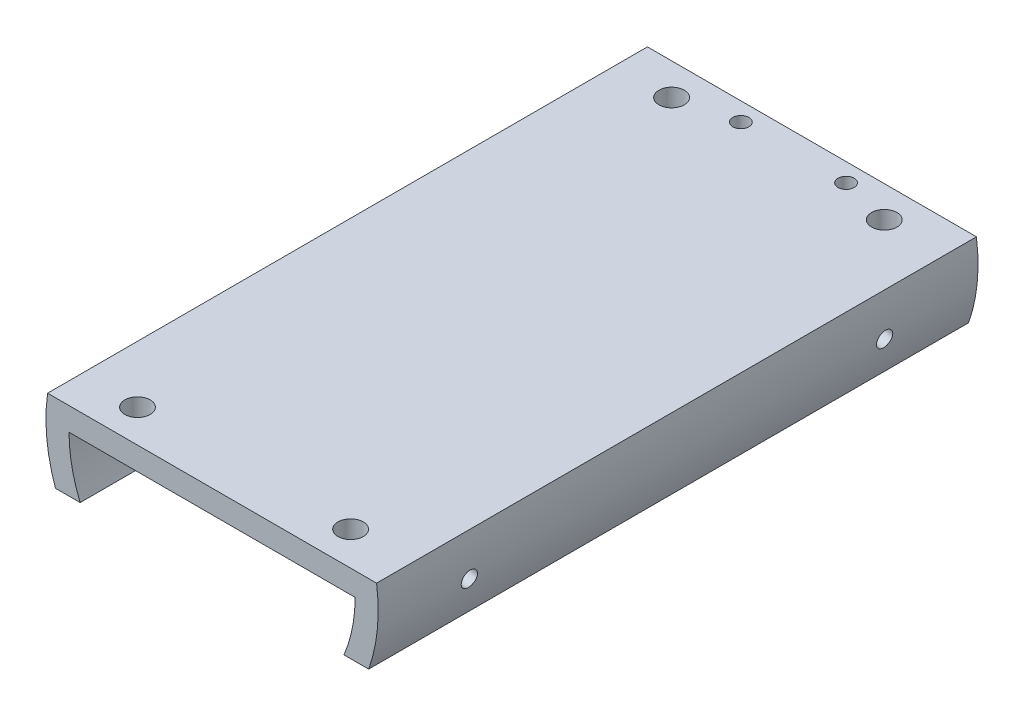
SolidWorks part; units mm, degrees
material "PET"
ref_plane "Front Plane" through (0, 0, 0) normal (0, 0, 1) x (1, 0, 0)
ref_plane "Top Plane" through (0, 0, 0) normal (0, 1, 0) x (1, 0, 0)
ref_plane "Right Plane" through (0, 0, 0) normal (1, 0, 0) x (0, 0, -1)
sketch "Sketch1" plane through (0, 0, 0) normal (0, 0, 1) x (1, 0, 0)
  line L0 (18, 0) -> (-18, 0)
  line L1 (18, 2.5) -> (-18, 2.5)
  line L2 (0, 0) -> (16.3135, -7.6071)
  line L3 (0, 0) -> (-16.3135, -7.6071)
  circle A0 centre (0, 0) radius 18
  circle A1 centre (0, 0) radius 15.5
  dimension "D1" = 36
  dimension "D4" = 25
  dimension "D5" = 25
  dimension "D2" = 2.5
  dimension "D3" = 2.5
extrude "Boss-Extrude1" add sketch "Sketch1" along normal blind 65 contours A1 L2 A0 L0 | A1 L0 A0 L1 | L0 A1 L1 | A1 L0 A0 L3 | A1 L1 A0 L0
sketch "Sketch2" plane through (0, 2.5, 0) normal (0, 1, 0) x (1, 0, 0)
  circle A0 centre (11.2395, -3.3946) radius 1.375
  circle A1 centre (-11.7605, -3.4431) radius 1.375
  circle A2 centre (11.3618, -61.3474) radius 1.375
  circle A3 centre (-11.638, -61.443) radius 1.375
  dimension "D1" = 2.75
  dimension "D2" = 2.75
  dimension "D3" = 2.75
  dimension "D4" = 2.75
extrude "Cut-Extrude1" cut sketch "Sketch2" against normal up to next
sketch "Sketch3" plane through (0, 0, 65) normal (0, 0, 1) x (1, 0, 0)
  line L0 (15.5, 0) -> (-15.5, 0) construction
  line L1 (-9, -6) -> (9, -6)
  line L2 (-9, -9) -> (9, -9)
  line L3 (-9, -9) -> (-9, 0)
  line L4 (-9, 0) -> (9, 0)
  line L5 (9, -9) -> (9, 0)
  circle A0 centre (0, -9) radius 9
  line M14 (-15.5, 0) -> (15.5, 0)
  dimension "D1" = 18
  dimension "D2" = 6
extrude "Boss-Extrude2" add sketch "Sketch3" against normal blind 65 contours A0 L3 L1 M14 | A0 L1 L5 L4
ref_plane "Plane1" through (-17.7265, -3.1257, 0) normal (-0.9848, -0.1736, 0) x (0, 0, -1)
sketch "Sketch4" [suppressed] plane through (-17.7265, -3.1257, 0) normal (-0.9848, -0.1736, 0) x (0, 0, -1)
  line L0 (-65, -5.5574) -> (0, -5.5574) construction
  line L1 (-65, 4.6587) -> (-65, -5.5574) construction
  circle A0 centre (-60, -1.5574) radius 0.875
  circle A1 centre (-5, -1.5574) radius 0.875
  dimension "D1" = 1.75
  dimension "D3" = 5
  dimension "D2" = 4
  dimension "D4" = 2
sketch "Sketch5" plane through (0, 2.5, 0) normal (0, 1, 0) x (1, 0, 0)
  circle A0 centre (-5.7, -2) radius 0.875
  circle A1 centre (5.7, -2) radius 0.875
  dimension "D1" = 1.75
  dimension "D2" = 1.75
extrude "Cut-Extrude3" cut sketch "Sketch5" against normal up to next
sketch "Sketch6" plane through (-17.7265, -3.1257, 0) normal (-0.9848, -0.1736, 0) x (0, 0, -1)
  line L0 (-65, -5.5574) -> (0, -5.5574) construction
  line L1 (-65, 4.6587) -> (-65, -5.5574) construction
  line L2 (0, -5.5574) -> (0, 4.6587) construction
  circle A0 centre (-55, -1.0574) radius 0.875
  circle A1 centre (-10, -1.0574) radius 0.875
  dimension "D1" = 1.75
  dimension "D3" = 10
  dimension "D4" = 1.75
  dimension "D2" = 4.5
  dimension "D5" = 10
  dimension "D6" = 4.5
extrude "Cut-Extrude4" cut sketch "Sketch6" against normal up to next
mirror "Mirror1" about plane through (0, 0, 0) normal (1, 0, 0) of "Cut-Extrude4"
ref_plane "Plane2" through (0, 0, 32.5) normal (0, 0, 1) x (1, 0, 0)
sketch "Sketch8" plane through (0, 0, 32.5) normal (0, 0, 1) x (1, 0, 0)
  line L0 (-16.9706, -6) -> (16.9706, -6)
  line L9 (14.0478, -6.5506) -> (16.3135, -7.6071)
  line L10 (17.8255, 2.5) -> (-17.8255, 2.5)
  line L11 (-16.3135, -7.6071) -> (-14.0478, -6.5506)
  line L12 (-15.5, 0) -> (-9, 0)
  line L13 (-9, 0) -> (-9, -6)
  line L14 (-9, -6) -> (-8.4853, -6)
  line L15 (8.4853, -6) -> (9, -6)
  line L16 (9, -6) -> (9, 0)
  line L17 (9, 0) -> (15.5, 0)
  line L18 (14.0478, -6.5506) -> (16.3135, -7.6071)
  line L19 (17.8255, 2.5) -> (-17.8255, 2.5)
  line L20 (-16.3135, -7.6071) -> (-14.0478, -6.5506)
  line L21 (-15.5, 0) -> (-9, 0)
  line L22 (-9, 0) -> (-9, -6)
  line L23 (-9, -6) -> (-8.4853, -6)
  line L24 (8.4853, -6) -> (9, -6)
  line L25 (9, -6) -> (9, 0)
  line L26 (9, 0) -> (15.5, 0)
  arc A5 (14.0478, -6.5506) -> (15.5, 0) centre (0, 0) ccw
  arc A6 (16.3135, -7.6071) -> (17.8255, 2.5) centre (0, 0) ccw
  arc A7 (-17.8255, 2.5) -> (-16.3135, -7.6071) centre (0, 0) ccw
  arc A8 (-15.5, 0) -> (-14.0478, -6.5506) centre (0, 0) ccw
  arc A9 (8.4853, -6) -> (-8.4853, -6) centre (0, -9) ccw
  arc A10 (14.0478, -6.5506) -> (15.5, 0) centre (0, 0) ccw
  arc A11 (16.3135, -7.6071) -> (17.8255, 2.5) centre (0, 0) ccw
  arc A12 (-17.8255, 2.5) -> (-16.3135, -7.6071) centre (0, 0) ccw
  arc A13 (-15.5, 0) -> (-14.0478, -6.5506) centre (0, 0) ccw
  arc A14 (8.4853, -6) -> (-8.4853, -6) centre (0, -9) ccw
  dimension "D1" = 0
extrude "Boss-Extrude3" add sketch "Sketch8" along normal mid plane 52 contours L21 A13 L0 L22 | L0 A10 L26 L25
sketch "Sketch9" plane through (0, 0, 65) normal (0, 0, 1) x (1, 0, 0)
  line L0 (-11.6458, -6) -> (16.9706, -6)
  line L1 (-14.2916, -6) -> (-9, -6) construction
  line L2 (-11.6458, -6) -> (-16.9706, -6)
  line L12 (14.0478, -6.5506) -> (16.3135, -7.6071)
  line L13 (17.8255, 2.5) -> (-17.8255, 2.5)
  line L14 (-16.3135, -7.6071) -> (-14.0478, -6.5506)
  line L15 (-15.5, 0) -> (-9, 0)
  line L16 (-9, 0) -> (-9, -6)
  line L17 (-9, -6) -> (-8.4853, -6)
  line L18 (8.4853, -6) -> (9, -6)
  line L19 (9, -6) -> (9, 0)
  line L20 (9, 0) -> (15.5, 0)
  line L21 (14.0478, -6.5506) -> (16.3135, -7.6071)
  line L22 (17.8255, 2.5) -> (-17.8255, 2.5)
  line L23 (-16.3135, -7.6071) -> (-14.0478, -6.5506)
  line L24 (-15.5, 0) -> (-9, 0)
  line L25 (-9, 0) -> (-9, -6)
  line L26 (-9, -6) -> (-8.4853, -6)
  line L27 (8.4853, -6) -> (9, -6)
  line L28 (9, -6) -> (9, 0)
  line L29 (9, 0) -> (15.5, 0)
  arc A0 (16.3135, -7.6071) -> (17.8255, 2.5) centre (0, 0) ccw construction
  arc A1 (-17.8255, 2.5) -> (-16.3135, -7.6071) centre (0, 0) ccw construction
  arc A7 (14.0478, -6.5506) -> (15.5, 0) centre (0, 0) ccw
  arc A8 (16.3135, -7.6071) -> (17.8255, 2.5) centre (0, 0) ccw
  arc A9 (-17.8255, 2.5) -> (-16.3135, -7.6071) centre (0, 0) ccw
  arc A10 (-15.5, 0) -> (-14.0478, -6.5506) centre (0, 0) ccw
  arc A11 (8.4853, -6) -> (-8.4853, -6) centre (0, -9) ccw
  arc A12 (14.0478, -6.5506) -> (15.5, 0) centre (0, 0) ccw
  arc A13 (16.3135, -7.6071) -> (17.8255, 2.5) centre (0, 0) ccw
  arc A14 (-17.8255, 2.5) -> (-16.3135, -7.6071) centre (0, 0) ccw
  arc A15 (-15.5, 0) -> (-14.0478, -6.5506) centre (0, 0) ccw
  arc A16 (8.4853, -6) -> (-8.4853, -6) centre (0, -9) ccw
  arc M15 (15.5, 0) -> (14.0478, -6.5506) centre (0, 0) cw
  line M16 (14.0478, -6.5506) -> (16.3135, -7.6071)
  arc M17 (16.3135, -7.6071) -> (17.8255, 2.5) centre (0, 0) ccw
  arc M19 (-17.8255, 2.5) -> (-16.3135, -7.6071) centre (0, 0) ccw
  line M20 (-16.3135, -7.6071) -> (-14.0478, -6.5506)
  arc M21 (-14.0478, -6.5506) -> (-15.5, 0) centre (0, 0) cw
  dimension "D1" = 0
extrude "Cut-Extrude7" cut sketch "Sketch9" against normal blind 69 contours L2 M21 M19 M20 | L0 M15 M16 M17
sketch "Sketch11" plane through (0, 0, 0) normal (0, -1, 0) x (-1, 0, 0)
  line L0 (-14.2916, 0) -> (-14.2916, -6.5) construction
  line L1 (14.2916, -65) -> (-14.2916, -65)
  line L2 (14.2916, -65) -> (14.2916, -58.5)
  line L3 (14.2916, -58.5) -> (-14.2916, -58.5)
  line L4 (-14.2916, -65) -> (-14.2916, -58.5)
  line L5 (-14.2916, -6.5) -> (14.2916, -6.5)
  line L6 (-14.2916, -6.5) -> (-14.2916, 0)
  line L7 (-14.2916, 0) -> (14.2916, 0)
  line L8 (14.2916, -6.5) -> (14.2916, 0)
extrude "Cut-Extrude8" cut sketch "Sketch11" along normal blind 69
